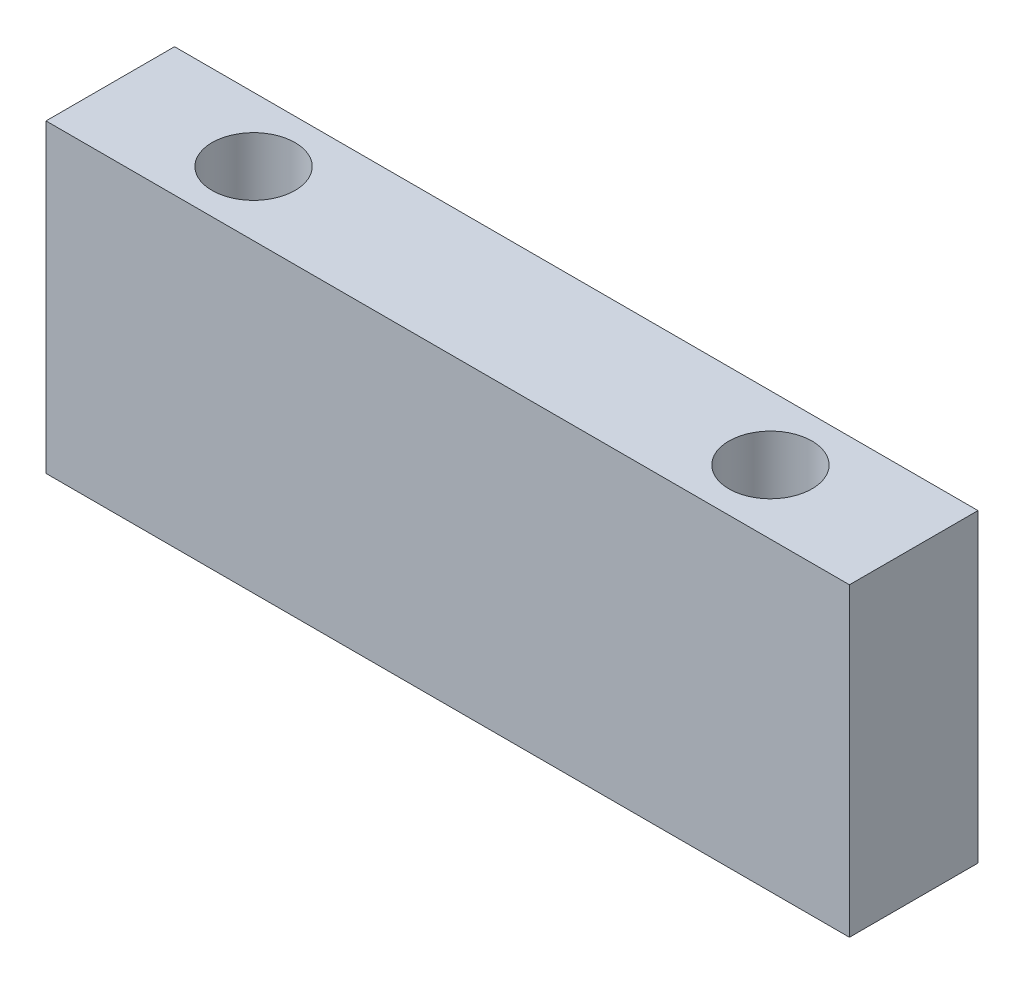
SolidWorks part; units mm, degrees
ref_plane "Front Plane" through (0, 0, 0) normal (0, 0, 1) x (1, 0, 0)
ref_plane "Top Plane" through (0, 0, 0) normal (0, 1, 0) x (1, 0, 0)
ref_plane "Right Plane" through (0, 0, 0) normal (1, 0, 0) x (0, 0, -1)
sketch "Sketch1" plane through (0, 0, 0) normal (0, 0, 1) x (1, 0, 0)
  line L0 (0, 0) -> (76.2, 0)
  line L1 (76.2, 0) -> (76.2, 28.956)
  line L2 (76.2, 28.956) -> (0, 28.956)
  line L3 (0, 28.956) -> (0, 0)
  dimension "D1" = 76.2
  dimension "D2" = 28.956
extrude "Boss-Extrude1" add sketch "Sketch1" along normal blind 12.192
sketch "Sketch2" plane through (0, 28.956, 0) normal (0, 1, 0) x (1, 0, 0)
  line L0 (0, -12.192) -> (0, 0) construction
  line L1 (76.2, -12.192) -> (76.2, 0) construction
  circle A0 centre (62.611, -6.096) radius 3.937
  circle A1 centre (13.589, -6.096) radius 3.937
  point P4 (0, -6.096)
  dimension "D1" = 7.874
  dimension "D2" = 7.874
  dimension "D3" = 13.589
  dimension "D4" = 13.589
extrude "Cut-Extrude1" cut sketch "Sketch2" against normal through all
